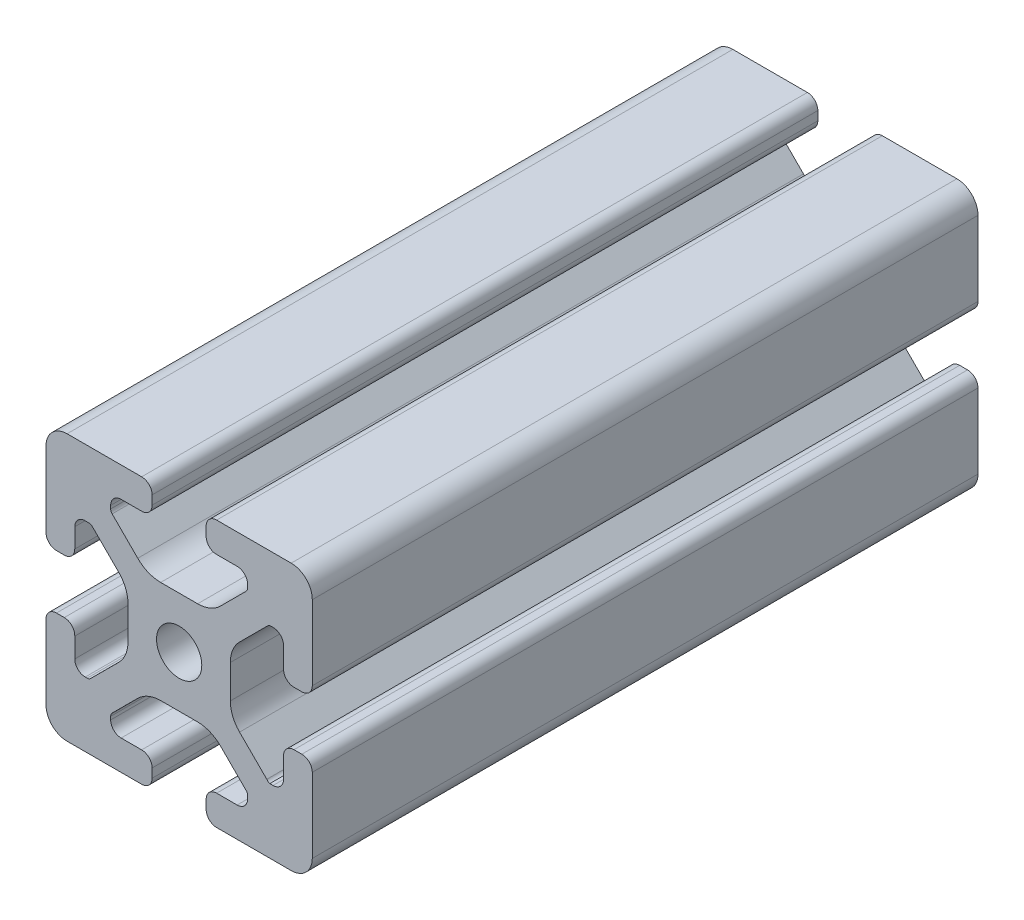
SolidWorks part; units mm, degrees
ref_plane "Front Plane" through (0, 0, 0) normal (0, 0, 1) x (1, 0, 0)
ref_plane "Top Plane" through (0, 0, 0) normal (0, 1, 0) x (1, 0, 0)
ref_plane "Right Plane" through (0, 0, 0) normal (1, 0, 0) x (0, 0, -1)
sketch "Sketch1" plane through (0, 0, 0) normal (0, 0, 1) x (1, 0, 0)
  line L0 (0, 19.7407) -> (0, -19.7407) construction
  line L1 (19.0335, 0) -> (-20.7246, 0) construction
  line L2 (-8.715, -15.5246) -> (-5.63, -15.5246)
  line L3 (-10.285, -13.9546) -> (-10.285, -13.4925)
  line L4 (-6.2171, -9.1098) -> (-10.0624, -12.9551)
  line L5 (2.7773, -7.685) -> (-2.7773, -7.685)
  line L6 (10.0624, -12.9551) -> (6.2171, -9.1098)
  line L7 (10.285, -13.9546) -> (10.285, -13.4925)
  line L8 (5.63, -15.5246) -> (8.715, -15.5246)
  line L9 (4.06, -18.43) -> (4.06, -17.0946)
  line L10 (-4.06, -18.43) -> (-4.06, -17.0946)
  line L11 (15.68, -8.7154) -> (15.68, -5.63)
  line L12 (-14.11, -10.2854) -> (-13.8169, -10.2854)
  line L13 (20, -16.83) -> (20, -5.63)
  line L14 (20, 5.63) -> (20, 13.0011)
  line L15 (-16.83, 20) -> (-5.63, 20)
  line L16 (5.63, 20) -> (12.9796, 20)
  line L17 (-8.715, 15.5246) -> (-5.63, 15.5246)
  line L18 (-20, -17.0184) -> (-20, -5.7579)
  line L19 (-20, 5.573) -> (-20, 13.0045)
  line L20 (-15.68, -8.7154) -> (-15.68, -5.7579)
  line L21 (-16.6746, -20) -> (-5.63, -20)
  line L22 (5.63, -20) -> (13, -20)
  line L23 (14.11, -10.2854) -> (13.6201, -10.2854)
  line L24 (13.1637, -9.947) -> (9.0762, -5.8595)
  line L25 (7.685, -2.5008) -> (7.685, 2.5008)
  line L26 (9.0762, 5.8595) -> (13.2795, 10.0628)
  line L27 (13.8169, 10.2854) -> (14.11, 10.2854)
  line L28 (15.68, 8.7154) -> (15.68, 5.63)
  line L29 (17.25, 4.06) -> (18.43, 4.06)
  line L30 (20, 13.0011) -> (20, 16.83)
  line L31 (16.83, 20) -> (12.9796, 20)
  line L32 (4.06, 18.43) -> (4.06, 17.0946)
  line L33 (5.63, 15.5246) -> (8.715, 15.5246)
  line L34 (10.285, 13.9546) -> (10.285, 13.4925)
  line L35 (10.0624, 12.9551) -> (6.2171, 9.1098)
  line L36 (2.7773, 7.685) -> (-2.7773, 7.685)
  line L37 (-6.2171, 9.1098) -> (-10.0624, 12.9551)
  line L38 (-10.285, 13.4925) -> (-10.285, 13.9546)
  line L39 (-4.06, 17.0946) -> (-4.06, 18.43)
  line L40 (-20, 16.83) -> (-20, 13.0045)
  line L41 (-18.43, 4.003) -> (-17.25, 4.003)
  line L42 (-15.68, 5.573) -> (-15.68, 8.4757)
  line L43 (-14.0552, 10.0447) -> (-13.7199, 10.033)
  line L44 (-13.0405, 9.8238) -> (-9.0762, 5.8595)
  line L45 (-7.685, 2.5008) -> (-7.685, -2.5008)
  line L46 (-9.0762, -5.8595) -> (-13.2795, -10.0628)
  line L47 (-17.2485, -4.1204) -> (-18.43, -4.1204)
  line L48 (13, -20) -> (16.83, -20)
  line L49 (18.43, -4.06) -> (17.25, -4.06)
  arc A0 (-5.63, -15.5246) -> (-4.06, -17.0946) centre (-5.63, -17.0946) cw
  arc A1 (-8.715, -15.5246) -> (-10.285, -13.9546) centre (-8.715, -13.9546) cw
  arc A2 (-10.285, -13.4925) -> (-10.0624, -12.9551) centre (-9.525, -13.4925) cw
  arc A3 (-6.2171, -9.1098) -> (-2.7773, -7.685) centre (-2.7773, -12.5496) cw
  arc A4 (2.7773, -7.685) -> (6.2171, -9.1098) centre (2.7773, -12.5496) cw
  arc A5 (10.0624, -12.9551) -> (10.285, -13.4925) centre (9.525, -13.4925) cw
  arc A6 (10.285, -13.9546) -> (8.715, -15.5246) centre (8.715, -13.9546) cw
  arc A7 (4.06, -17.0946) -> (5.63, -15.5246) centre (5.63, -17.0946) cw
  arc A8 (5.63, -20) -> (4.06, -18.43) centre (5.63, -18.43) cw
  arc A9 (-4.06, -18.43) -> (-5.63, -20) centre (-5.63, -18.43) cw
  circle A10 centre (0, 0) radius 3.4
  arc A11 (17.25, -4.06) -> (15.68, -5.63) centre (17.25, -5.63) ccw
  arc A12 (14.11, -10.2854) -> (15.68, -8.7154) centre (14.11, -8.7154) ccw
  arc A13 (13.1637, -9.947) -> (13.6201, -10.2854) centre (13.8117, -9.55) ccw
  arc A14 (7.685, -2.5008) -> (9.0762, -5.8595) centre (12.435, -2.5008) ccw
  arc A15 (9.0762, 5.8595) -> (7.685, 2.5008) centre (12.435, 2.5008) ccw
  arc A16 (13.8169, 10.2854) -> (13.2795, 10.0628) centre (13.8169, 9.5254) ccw
  arc A17 (15.68, 8.7154) -> (14.11, 10.2854) centre (14.11, 8.7154) ccw
  arc A18 (15.68, 5.63) -> (17.25, 4.06) centre (17.25, 5.63) ccw
  arc A19 (18.43, 4.06) -> (20, 5.63) centre (18.43, 5.63) ccw
  arc A20 (20, 16.83) -> (16.83, 20) centre (16.83, 16.83) ccw
  arc A21 (5.63, 20) -> (4.06, 18.43) centre (5.63, 18.43) ccw
  arc A22 (4.06, 17.0946) -> (5.63, 15.5246) centre (5.63, 17.0946) ccw
  arc A23 (10.285, 13.9546) -> (8.715, 15.5246) centre (8.715, 13.9546) ccw
  arc A24 (10.0624, 12.9551) -> (10.285, 13.4925) centre (9.525, 13.4925) ccw
  arc A25 (2.7773, 7.685) -> (6.2171, 9.1098) centre (2.7773, 12.5496) ccw
  arc A26 (-6.2171, 9.1098) -> (-2.7773, 7.685) centre (-2.7773, 12.5496) ccw
  arc A27 (-10.285, 13.4925) -> (-10.0624, 12.9551) centre (-9.525, 13.4925) ccw
  arc A28 (-8.715, 15.5246) -> (-10.285, 13.9546) centre (-8.715, 13.9546) ccw
  arc A29 (-5.63, 15.5246) -> (-4.06, 17.0946) centre (-5.63, 17.0946) ccw
  arc A30 (-4.06, 18.43) -> (-5.63, 20) centre (-5.63, 18.43) ccw
  arc A31 (-16.83, 20) -> (-20, 16.83) centre (-16.83, 16.83) ccw
  arc A32 (-20, 5.573) -> (-18.43, 4.003) centre (-18.43, 5.573) ccw
  arc A33 (-17.25, 4.003) -> (-15.68, 5.573) centre (-17.25, 5.573) ccw
  arc A34 (-14.0552, 10.0447) -> (-15.68, 8.4757) centre (-14.11, 8.4757) ccw
  arc A35 (-13.0405, 9.8238) -> (-13.7199, 10.033) centre (-13.5779, 9.2864) ccw
  arc A36 (-7.685, 2.5008) -> (-9.0762, 5.8595) centre (-12.435, 2.5008) ccw
  arc A37 (-9.0762, -5.8595) -> (-7.685, -2.5008) centre (-12.435, -2.5008) ccw
  arc A38 (-13.8169, -10.2854) -> (-13.2795, -10.0628) centre (-13.8169, -9.5254) ccw
  arc A39 (-15.68, -8.7154) -> (-14.11, -10.2854) centre (-14.11, -8.7154) ccw
  arc A40 (-15.68, -5.7579) -> (-17.2485, -4.1204) centre (-17.2485, -5.6904) ccw
  arc A41 (-18.43, -4.1204) -> (-20, -5.7579) centre (-18.4315, -5.6904) ccw
  arc A42 (-20, -17.0184) -> (-16.6746, -20) centre (-16.8354, -16.8341) ccw
  arc A43 (16.83, -20) -> (20, -16.83) centre (16.83, -16.83) ccw
  arc A44 (20, -5.63) -> (18.43, -4.06) centre (18.43, -5.63) ccw
  dimension "D1" = 6.8
  dimension "D2" = 4.32
  dimension "D3" = 15.37
  dimension "D4" = 20.57
  dimension "D5" = 15.37
  dimension "D6" = 40
  dimension "D7" = 20
  dimension "D8" = 4.32
  dimension "D9" = 8.12
extrude "Boss-Extrude1" add sketch "Sketch1" along normal blind 100
